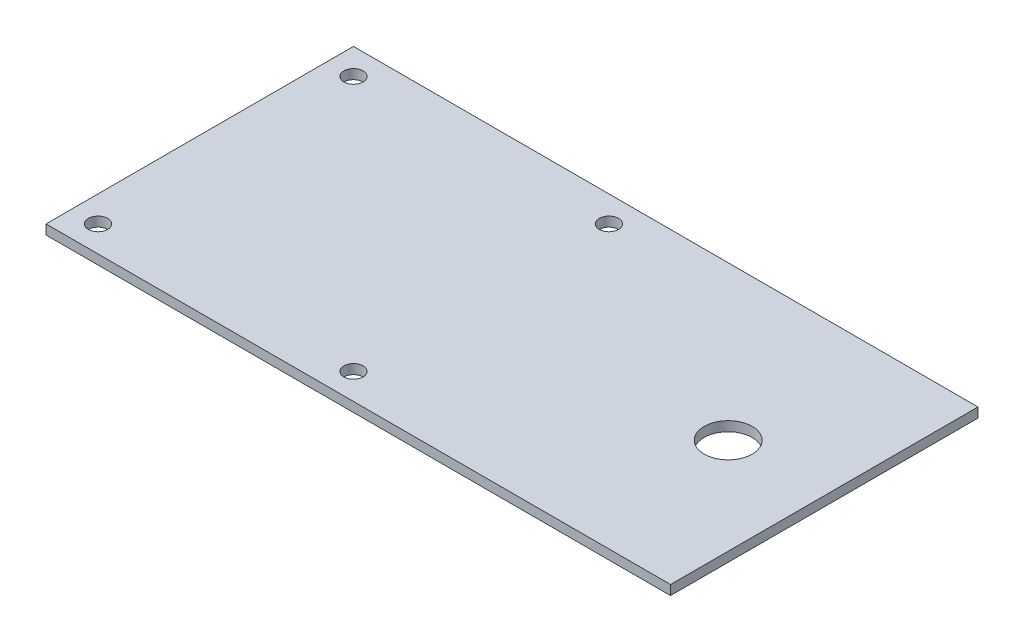
SolidWorks part; units mm, degrees
material "ASTM A36 Acero"
ref_plane "Alzado" through (0, 0, 0) normal (0, 0, 1) x (1, 0, 0)
ref_plane "Planta" through (0, 0, 0) normal (0, 1, 0) x (1, 0, 0)
ref_plane "Vista lateral" through (0, 0, 0) normal (1, 0, 0) x (0, 0, -1)
sketch "Croquis1" plane through (0, 0, 0) normal (0, 1, 0) x (1, 0, 0)
  line L1 (-300, -160) -> (350, -160)
  line L3 (-300, 160) -> (350, 160)
  line L4 (350, -160) -> (350, 160)
  line L14 (-300, -160) -> (-300, 160)
  circle A1 centre (-272.9361, 132.9361) radius 10
  circle A2 centre (-7.0639, 132.9361) radius 10
  circle A3 centre (-7.0639, -132.9361) radius 10
  circle A4 centre (-272.9361, -132.9361) radius 10
  circle A5 centre (250, 0) radius 25
  point P0 (0, 0)
  dimension "D3" = 50
  dimension "D5" = 20
  dimension "D1" = 320
  dimension "D2" = 650
  dimension "D4" = 100
  dimension "D6" = 4
extrude "Saliente-Extruir1" add sketch "Croquis1" along normal blind 10
